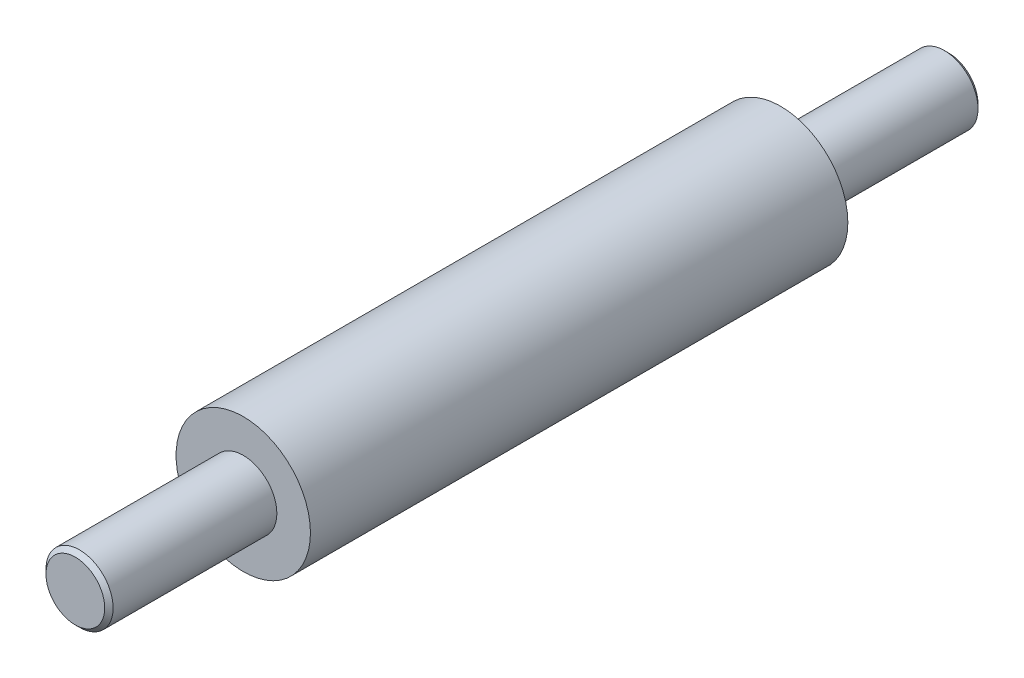
SolidWorks part; units mm, degrees
material "XC38"
ref_plane "Face" through (0, 0, 0) normal (0, 0, 1) x (1, 0, 0)
ref_plane "Dessus" through (0, 0, 0) normal (0, 1, 0) x (1, 0, 0)
ref_plane "Droite" through (0, 0, 0) normal (1, 0, 0) x (0, 0, -1)
sketch "Esquisse1" plane through (0, 0, 0) normal (0, 0, 1) x (1, 0, 0)
  circle A0 centre (0, 0) radius 4
  dimension "D1" = 8
extrude "Boss.-Extru.1" add sketch "Esquisse1" along normal mid plane 32
sketch "Esquisse2" plane through (0, 0, 16) normal (0, 0, 1) x (1, 0, 0)
  circle A0 centre (0, 0) radius 2
  dimension "D1" = 4
extrude "Boss.-Extru.2" add sketch "Esquisse2" along normal blind 10
cosmetic thread "Représentation de filetage1" parameters "D1"=8, "D2"=3
chamfer "Chanfrein1" distance 0.25 angle 45 1 edges at (2, 0, 26)
mirror "Symétrie1" about plane through (0, 0, 0) normal (0, 0, 1) of "Chanfrein1", "Boss.-Extru.2"
